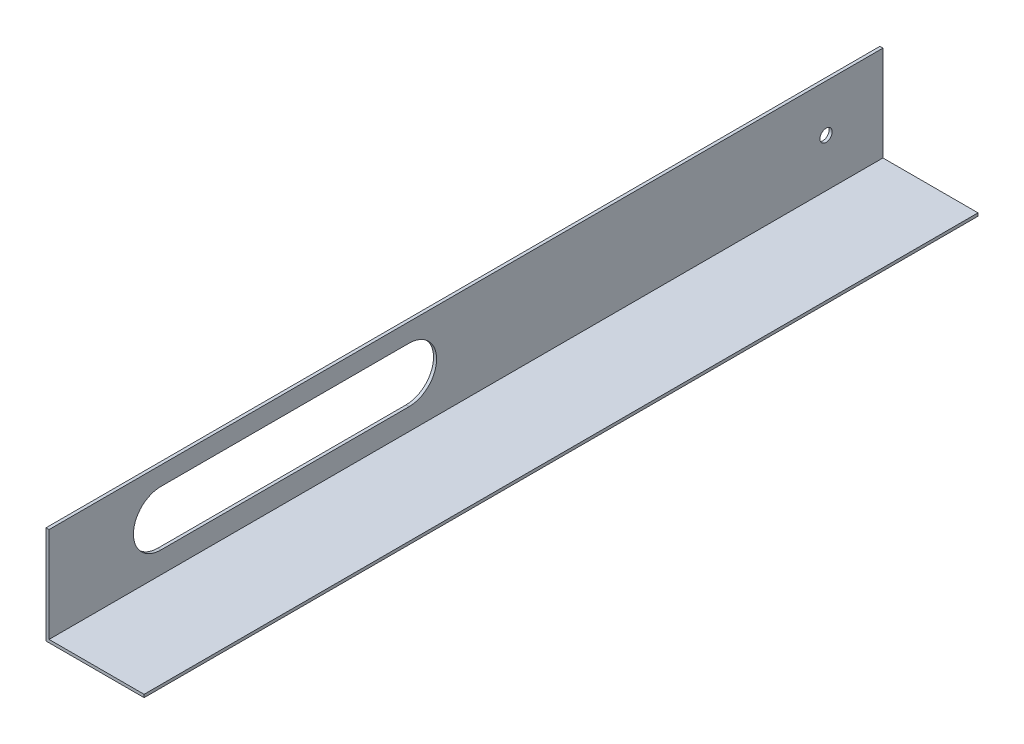
SolidWorks part; units mm, degrees
ref_plane "Front Plane" through (0, 0, 0) normal (0, 0, 1) x (1, 0, 0)
ref_plane "Top Plane" through (0, 0, 0) normal (0, 1, 0) x (1, 0, 0)
ref_plane "Right Plane" through (0, 0, 0) normal (1, 0, 0) x (0, 0, -1)
sketch "Sketch3" plane through (0, 0, 0) normal (0, 0, 1) x (1, 0, 0)
  line L20 (49.2125, 1.5875) -> (49.2125, 50.8)
  line L21 (49.2125, 50.8) -> (50.8, 50.8)
  line L22 (50.8, 50.8) -> (50.8, 1.524)
  line L24 (50.8, 1.524) -> (100.0125, 1.524)
  line L25 (100.0125, 1.524) -> (100.0125, 0)
  line L26 (100.0125, 0) -> (49.2125, 0)
  line L27 (49.2125, 0) -> (49.2125, 1.5875)
  dimension "D1" = 50.8
  dimension "D2" = 1.524
  dimension "D3" = 1.5875
  dimension "D4" = 50.8
extrude "Boss-Extrude2" add sketch "Sketch3" along normal blind 431.8
sketch "Sketch8" plane through (50.8, 0, 0) normal (1, 0, 0) x (0, 0, -1)
  line L0 (-431.8, 50.8) -> (-431.8, 0) construction
  line L1 (-245.364, 26.924) -> (-373.888, 26.924) construction
  line L2 (-245.364, 12.7) -> (-373.888, 12.7)
  line L3 (-245.364, 41.148) -> (-373.888, 41.148)
  line L4 (-431.8, 50.8) -> (0, 50.8) construction
  line L5 (0, 1.524) -> (0, 50.8) construction
  line L7 (-431.8, 50.8) -> (0, 50.8) construction
  arc A1 (-245.364, 12.7) -> (-245.364, 41.148) centre (-245.364, 26.924) ccw
  arc A2 (-373.888, 41.148) -> (-373.888, 12.7) centre (-373.888, 26.924) ccw
  circle A3 centre (-29.464, 26.416) radius 3.175
  point P1 (-388.112, 26.924)
  point P6 (-309.626, 26.924)
  point P11 (-231.14, 26.924)
  dimension "D1" = 156.972
  dimension "D2" = 43.688
  dimension "D4" = 6.35
  dimension "D3" = 28.448
  dimension "D5" = 29.464
  dimension "D6" = 24.384
  dimension "D7" = 9.652
extrude "Cut-Extrude6" cut sketch "Sketch8" against normal blind 2.54
ref_plane "Plane1" through (241.3, 0, 0) normal (1, 0, 0) x (0, 0, -1)
